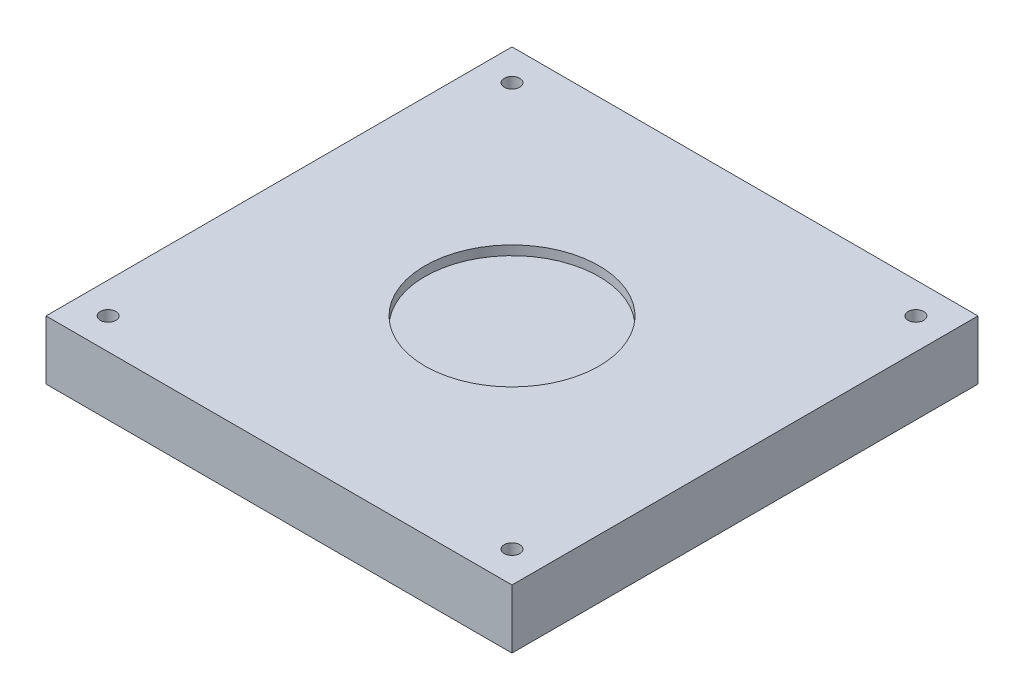
SolidWorks part; units mm, degrees
ref_plane "Front Plane" through (0, 0, 0) normal (0, 0, 1) x (1, 0, 0)
ref_plane "Top Plane" through (0, 0, 0) normal (0, 1, 0) x (1, 0, 0)
ref_plane "Right Plane" through (0, 0, 0) normal (1, 0, 0) x (0, 0, -1)
sketch "Sketch1" plane through (0, 0, 0) normal (0, 1, 0) x (1, 0, 0)
  line L1 (0, 0) -> (150, 0)
  line L2 (0, 0) -> (0, 150)
  line L3 (0, 150) -> (150, 150)
  line L4 (150, 0) -> (150, 150)
  dimension "D1" = 150
  dimension "D2" = 150
extrude "Boss-Extrude1" add sketch "Sketch1" along normal blind 19
sketch "Sketch2" plane through (0, 19, 0) normal (0, 1, 0) x (1, 0, 0)
  line L0 (75, 150) -> (75, 0) construction
  line L1 (150, 150) -> (0, 150) construction
  line L2 (0, 0) -> (150, 0) construction
  circle A0 centre (75, 75) radius 28
  dimension "D1" = 56
extrude "Cut-Extrude1" cut sketch "Sketch2" against normal blind 3
sketch "Sketch4" plane through (0, 19, 0) normal (0, 1, 0) x (1, 0, 0)
  line L0 (150, 150) -> (0, 150) construction
  line L1 (0, 150) -> (0, 0) construction
  line L2 (75, 150) -> (75, 0) construction
  line L3 (0, 0) -> (150, 0) construction
  line L4 (0, 75) -> (150, 75) construction
  line L5 (150, 0) -> (150, 150) construction
  circle A0 centre (10, 140) radius 2.5
  circle A1 centre (140, 140) radius 2.5
  circle A2 centre (140, 10) radius 2.5
  circle A3 centre (10, 10) radius 2.5
  dimension "D1" = 5
  dimension "D2" = 10
  dimension "D3" = 10
extrude "Cut-Extrude2" cut sketch "Sketch4" against normal blind 6.35
